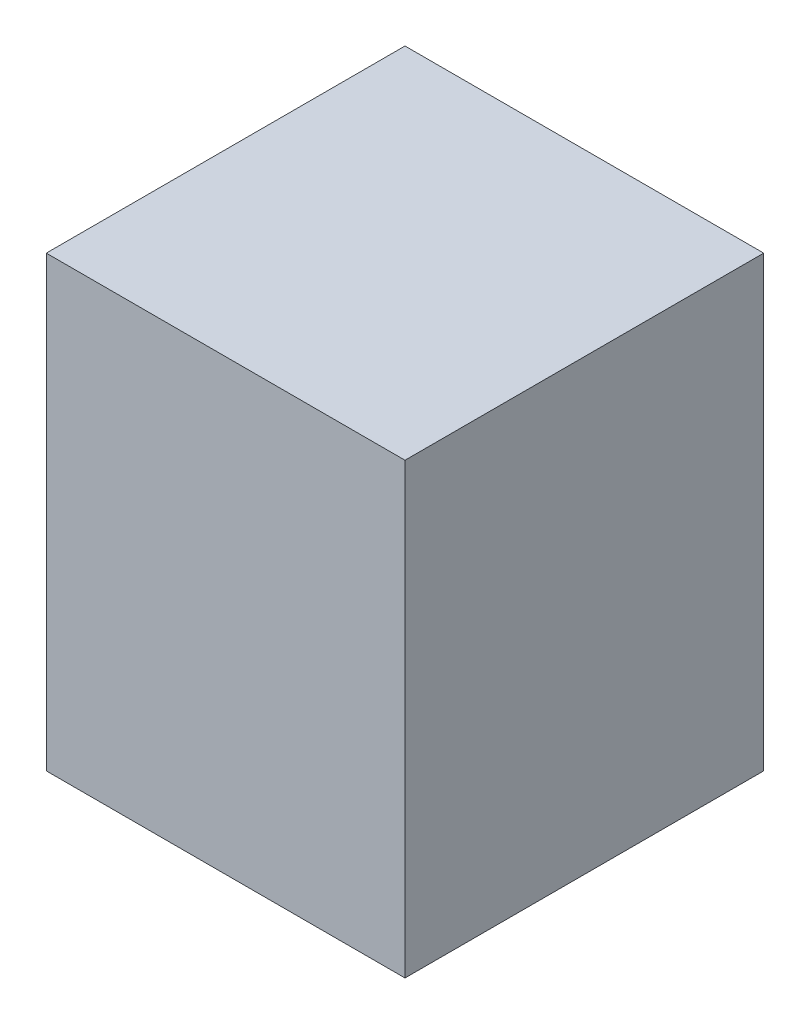
SolidWorks part; units mm, degrees
material "Polyethylene Cross-Linked"
ref_plane "Front Plane" through (0, 0, 0) normal (0, 0, 1) x (1, 0, 0)
ref_plane "Top Plane" through (0, 0, 0) normal (0, 1, 0) x (1, 0, 0)
ref_plane "Right Plane" through (0, 0, 0) normal (1, 0, 0) x (0, 0, -1)
sketch "Sketch1" plane through (0, 0, 0) normal (0, 1, 0) x (1, 0, 0)
  line L1 (0, 0) -> (12.7, 0)
  line L2 (0, 0) -> (0, 12.7)
  line L3 (0, 12.7) -> (12.7, 12.7)
  line L4 (12.7, 0) -> (12.7, 12.7)
extrude "Boss-Extrude1" add sketch "Sketch1" along normal blind 15.875
